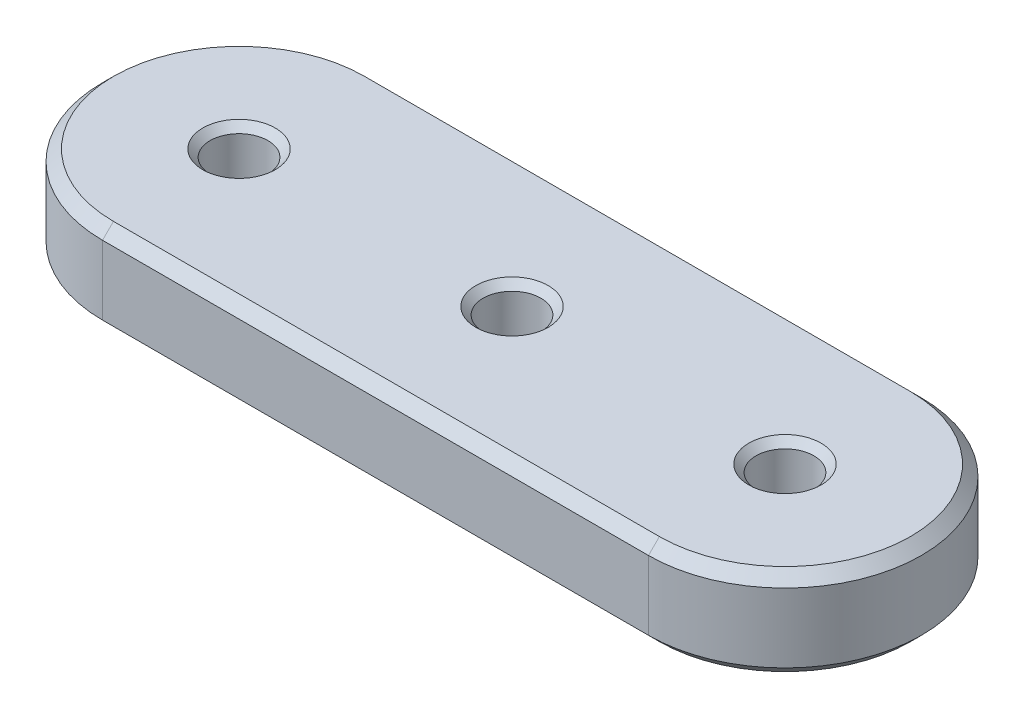
SolidWorks part; units mm, degrees
ref_plane "Front" through (0, 0, 0) normal (0, 0, 1) x (1, 0, 0)
ref_plane "Top" through (0, 0, 0) normal (0, 1, 0) x (1, 0, 0)
ref_plane "Right" through (0, 0, 0) normal (1, 0, 0) x (0, 0, -1)
sketch "Sketch10" plane through (0, 0, 0) normal (0, 1, 0) x (1, 0, 0)
  line L0 (-19.05, 0) -> (19.05, 0) construction
  line L1 (-19.05, 9.525) -> (19.05, 9.525)
  line L2 (-19.05, -9.525) -> (19.05, -9.525)
  arc A0 (-19.05, 9.525) -> (-19.05, -9.525) centre (-19.05, 0) ccw
  arc A1 (19.05, -9.525) -> (19.05, 9.525) centre (19.05, 0) ccw
  point P2 (0, 0)
  dimension "D1" = 19.05
  dimension "D2" = 38.1
extrude "Boss-Extrude2" add sketch "Sketch10" along normal mid plane 6.35 contours L1 A1 L2 A0
hole_wizard "#10-32 Tapped Hole2" positions "Sketch15" profile "Sketch16" tap size "#10-32" standard "ANSI Inch" end condition up to next
sketch "Sketch15" plane through (0, 3.175, 0) normal (0, 1, 0) x (1, 0, 0)
  arc A0 (19.05, -9.525) -> (19.05, 9.525) centre (19.05, 0) ccw construction
  arc A1 (-19.05, 9.525) -> (-19.05, -9.525) centre (-19.05, 0) ccw construction
  point P0 (19.05, 0)
  point P7 (-19.05, 0)
  point P9 (0, 0)
  point P11 (0, 0)
  point P13 (0, 0)
sketch "Sketch16" plane through (19.05, 3.175, 0) normal (1, 0, 0) x (0, 0, 1)
  line L0 (0, 0) -> (0, 6.35)
  line L1 (0, 6.35) -> (2.0193, 6.35)
  line L2 (2.0193, 6.35) -> (2.0193, 0)
  line L5 (2.0193, 0) -> (0, 0)
  line L11 (0, -6.35) -> (0, 107.95) construction
  dimension "Thru Tap Drill Dia." = 4.0386
  dimension "Thru Tap Drill Depth" = 6.35
cosmetic thread "Hole Thread15" parameters "D2"=4.826
cosmetic thread "Hole Thread16" parameters "D2"=4.826
cosmetic thread "Hole Thread17" parameters "D2"=4.826
chamfer "Chamfer4" distance 0.762 angle 45 8 edges at (0, 3.175, -9.525) (-28.575, 3.175, 0) (28.575, 3.175, 0) (0, 3.175, 9.525) (0, -3.175, -9.525) (-28.575, -3.175, 0) (28.575, -3.175, 0) (0, -3.175, 9.525)
chamfer "Chamfer5" distance 0.508 angle 45 6 edges at (19.05, 3.175, 2.0193) (19.05, -3.175, 2.0193) (0, 3.175, 2.0193) (0, -3.175, 2.0193) (-19.05, 3.175, 2.0193) (-19.05, -3.175, 2.0193)
